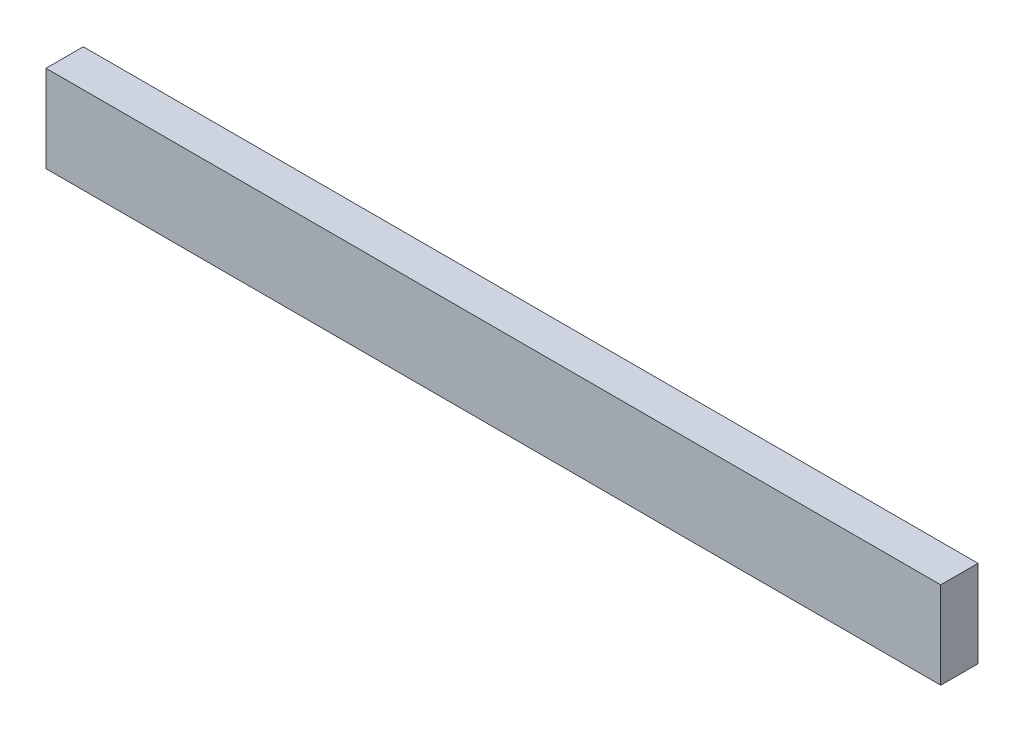
SolidWorks part; units mm, degrees
material "Oak"
ref_plane "Front Plane" through (0, 0, 0) normal (0, 0, 1) x (1, 0, 0)
ref_plane "Top Plane" through (0, 0, 0) normal (0, 1, 0) x (1, 0, 0)
ref_plane "Right Plane" through (0, 0, 0) normal (1, 0, 0) x (0, 0, -1)
sketch "Sketch1" plane through (0, 0, 0) normal (1, 0, 0) x (0, 0, -1)
  line L1 (-19.05, -44.45) -> (19.05, -44.45)
  line L2 (-19.05, -44.45) -> (-19.05, 44.45)
  line L3 (-19.05, 44.45) -> (19.05, 44.45)
  line L4 (19.05, -44.45) -> (19.05, 44.45)
  line L5 (-19.05, -44.45) -> (19.05, 44.45) construction
  line L6 (-19.05, 44.45) -> (19.05, -44.45) construction
  point P0 (0, 0)
  dimension "D1" = 38.1
  dimension "D2" = 88.9
extrude "Boss-Extrude1" add sketch "Sketch1" along normal blind 914.4
